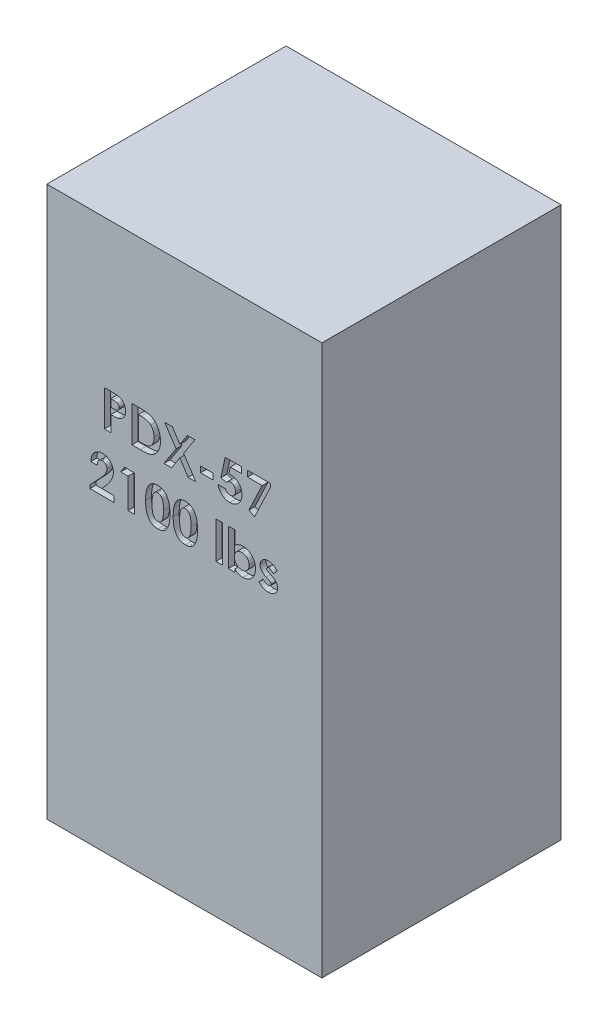
SolidWorks part; units mm, degrees
ref_plane "Front Plane" through (0, 0, 0) normal (0, 0, 1) x (1, 0, 0)
ref_plane "Top Plane" through (0, 0, 0) normal (0, 1, 0) x (1, 0, 0)
ref_plane "Right Plane" through (0, 0, 0) normal (1, 0, 0) x (0, 0, -1)
sketch "Sketch1" plane through (0, 0, 0) normal (0, 0, 1) x (1, 0, 0)
  line L1 (292.1, 584.2) -> (-292.1, 584.2)
  line L2 (292.1, 584.2) -> (292.1, -584.2)
  line L3 (292.1, -584.2) -> (-292.1, -584.2)
  line L4 (-292.1, 584.2) -> (-292.1, -584.2)
  line L5 (292.1, 584.2) -> (-292.1, -584.2) construction
  line L6 (292.1, -584.2) -> (-292.1, 584.2) construction
  point P0 (0, 0)
  dimension "D1" = 1168.4
  dimension "D2" = 584.2
extrude "Boss-Extrude1" add sketch "Sketch1" along normal blind 508
sketch "Sketch2" plane through (0, 0, 508) normal (0, 0, 1) x (1, 0, 0)
  line L0 (-292.1, 194.7333) -> (292.1, 194.7333) construction
  line L1 (-292.1, 584.2) -> (-292.1, -584.2) construction
  line L2 (292.1, -584.2) -> (292.1, 584.2) construction
  line L3 (292.1, 584.2) -> (-292.1, 584.2) construction
  text T0 "<b>PDX-57</b>\r\n<b>2100 lbs</b>\r\n" font "Century Gothic" height 76.2
  dimension "D1" = 389.4667
extrude "Cut-Extrude1" cut sketch "Sketch2" against normal blind 12.7
